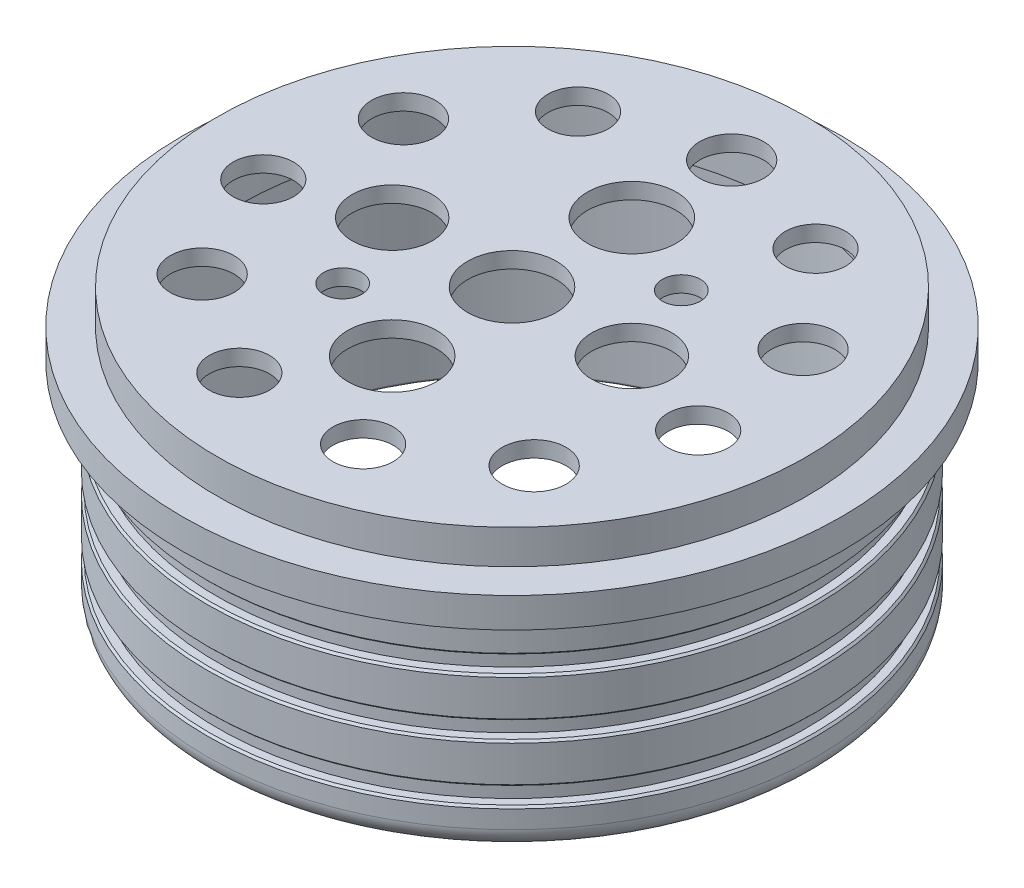
SolidWorks part; units mm, degrees
ref_plane "Front Plane" through (0, 0, 0) normal (0, 0, 1) x (1, 0, 0)
ref_plane "Top Plane" through (0, 0, 0) normal (0, 1, 0) x (1, 0, 0)
ref_plane "Right Plane" through (0, 0, 0) normal (1, 0, 0) x (0, 0, -1)
sketch "Sketch1" plane through (0, 0, 0) normal (0, 1, 0) x (1, 0, 0)
  circle A0 centre (0, 0) radius 69.75
  circle A1 centre (0, 0) radius 76.25
  dimension "D1" = 152.5
  dimension "D2" = 139.5
sketch "Sketch2" plane through (0, 0, 0) normal (0, 0, 1) x (1, 0, 0)
  line L0 (0, 0) -> (76.25, 0) construction
  line L1 (76.25, 0) -> (-76.25, 0) construction
  line L2 (0, 0) -> (0, 52.75) construction
  line L3 (0, 52.75) -> (69.75, 52.75) construction
  line L4 (76.25, 52.75) -> (76.25, 42.75)
  line L5 (69.75, 0) -> (69.75, 52.75)
  line L6 (69.75, 0) -> (-69.75, 0) construction
  line L8 (69.75, 0) -> (76.25, 0)
  line L10 (73.75, 42.75) -> (73.75, 38.5)
  line L12 (76.25, 38.5) -> (76.25, 28.5)
  line L14 (73.75, 28.5) -> (73.75, 24.25)
  line L16 (76.25, 24.25) -> (76.25, 14.25)
  line L18 (73.75, 14.25) -> (73.75, 10)
  line L20 (76.25, 10) -> (76.25, 0)
  line L21 (0, 52.75) -> (69.75, 52.75)
  line L22 (82.55, 52.75) -> (82.55, 60.25)
  line L23 (82.55, 60.25) -> (73.75, 60.25)
  line L24 (0, 60.25) -> (0, 52.75)
  line L25 (0, 60.25) -> (0, 68.8102)
  line L26 (0, 68.8102) -> (73.75, 68.8102)
  line L27 (73.75, 68.8102) -> (73.75, 60.25)
  line L28 (76.25, 52.75) -> (82.55, 52.75)
  line L29 (76.25, 42.75) -> (73.75, 42.75)
  line L30 (73.75, 38.5) -> (76.25, 38.5)
  line L31 (73.75, 28.5) -> (76.25, 28.5)
  line L32 (73.75, 24.25) -> (76.25, 24.25)
  line L33 (73.75, 14.25) -> (76.25, 14.25)
  line L34 (73.75, 10) -> (76.25, 10)
  dimension "D1" = 52.75
  dimension "D2" = 76.25
  dimension "D3" = 6.5
  dimension "D4" = 10
  dimension "D5" = 4.25
  dimension "D6" = 8.8
  dimension "D8" = 2.5
  dimension "D12" = 2.5
  dimension "D13" = 10
  dimension "D17" = 2.5
  dimension "D18" = 10
  dimension "D19" = 7.5
  dimension "D20" = 82.55
  dimension "D21" = 73.75
  dimension "D23" = 68.8102
revolve "Revolve1" add sketch "Sketch2" angle 360 about L2
chamfer "Chamfer1" distance 0.5 angle 45 6 edges at (0, 10, -76.25) (0, 14.25, -76.25) (0, 24.25, -76.25) (0, 28.5, -76.25) (0, 42.75, -76.25) (0, 38.5, -76.25)
fillet "Fillet3" radius 5 1 edges at (0, 0, -76.25)
fillet "Fillet4" radius 0.5 1 edges at (0, 0, -69.75)
sketch "Sketch3" plane through (0, 68.8102, 0) normal (0, 1, 0) x (1, 0, 0)
  line L0 (0, 0) -> (86.7831, 80.9265) construction
  line L1 (0, 0) -> (138.5384, 0) construction
  line L2 (0, 0) -> (-64.7388, 69.4238) construction
  circle A0 centre (0, 0) radius 11.125
  circle A1 centre (30, 0) radius 10.05
  circle A2 centre (0, -30) radius 11.125
  circle A3 centre (-30, 0) radius 10.05
  circle A4 centre (0, 30) radius 11.125
  circle A5 centre (0, 55) radius 8
  circle A6 centre (29.7352, 46.2689) radius 7.55
  circle A7 centre (50.0298, 22.8478) radius 8
  circle A8 centre (54.4402, -7.8273) radius 7.55
  circle A9 centre (41.5662, -36.0173) radius 8
  circle A10 centre (15.4953, -52.7721) radius 7.55
  circle A11 centre (-15.4953, -52.7721) radius 7.55
  circle A12 centre (-41.5662, -36.0173) radius 8
  circle A13 centre (-54.4402, -7.8273) radius 7.55
  circle A14 centre (-50.0298, 22.8478) radius 8
  circle A15 centre (-29.7352, 46.2689) radius 7.55
  circle A16 centre (0, 0) radius 73.75 construction
  circle A17 centre (21.9406, 20.46) radius 4.7625
  circle A18 centre (-21.9406, -20.46) radius 4.7625
  point P14 (0, 0)
  point P36 (0, 0)
  dimension "D1" = 22.25
  dimension "D2" = 20.1
  dimension "D4" = 16
  dimension "D6" = 15.1
  dimension "D25" = 43
  dimension "D26" = 9.525
  dimension "D3" = 30
  dimension "D5" = 25
  dimension "D7" = 15.4953
  dimension "D8" = 29.7352
  dimension "D9" = 41.5662
  dimension "D10" = 50.0298
  dimension "D11" = 54.4402
  dimension "D12" = 15.4953
  dimension "D13" = 29.7352
  dimension "D14" = 30
  dimension "D15" = 41.5662
  dimension "D16" = 50.0298
  dimension "D17" = 54.4402
  dimension "D18" = 22.8478
  dimension "D19" = 30
  dimension "D20" = 46.2689
  dimension "D21" = 7.8273
  dimension "D22" = 30
  dimension "D23" = 36.0173
  dimension "D24" = 52.7721
  dimension "D27" = 30
extrude "Cut-Extrude1" cut sketch "Sketch3" against normal up to next
sketch "Sketch4" plane through (0, 52.75, 0) normal (0, -1, 0) x (1, 0, 0)
  circle A0 centre (0, 0) radius 68
extrude "Cut-Extrude2" cut sketch "Sketch4" against normal blind 12.06
